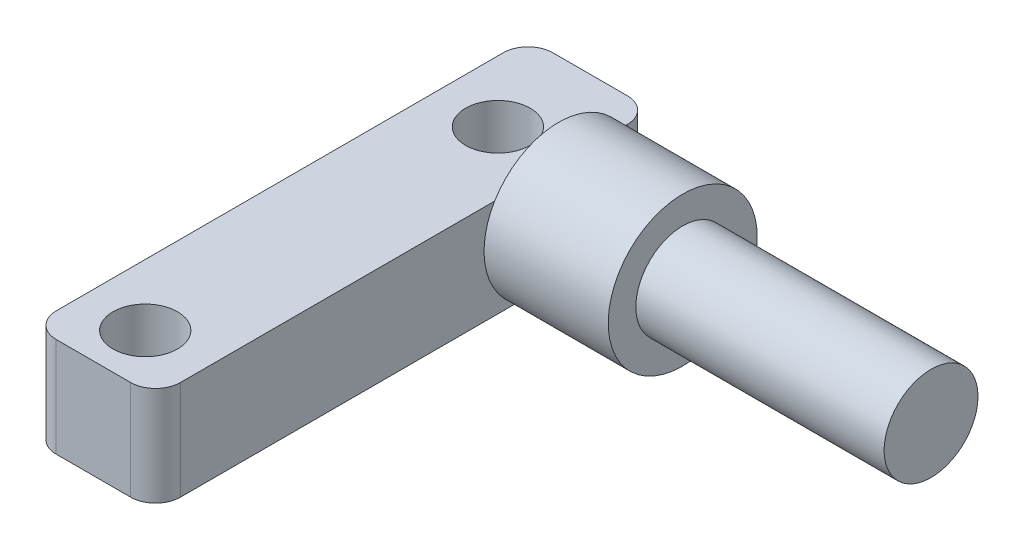
SolidWorks part; units mm, degrees
ref_plane "Front Plane" through (0, 0, 0) normal (0, 0, 1) x (1, 0, 0)
ref_plane "Top Plane" through (0, 0, 0) normal (0, 1, 0) x (1, 0, 0)
ref_plane "Right Plane" through (0, 0, 0) normal (1, 0, 0) x (0, 0, -1)
sketch "Sketch1" plane through (0, 0, 0) normal (0, 1, 0) x (1, 0, 0)
  line L0 (-3.5227, -7.2529) -> (-3.5227, -32.6529)
extrude "Extrude-Thin1" add sketch "Sketch1" along normal blind 5.08 thin contours L0 thin type one direction reverse wall 6.35
fillet "Fillet4" radius 1.27 1 edges at (-3.5227, 2.54, 32.6529)
fillet "Fillet5" radius 1.27 1 edges at (2.8273, 2.54, 32.6529)
fillet "Fillet6" radius 1.27 2 edges at (-3.5227, 2.54, 7.2529) (2.8273, 2.54, 7.2529)
sketch "Sketch5" plane through (0, 5.08, 0) normal (0, 1, 0) x (1, 0, 0)
  circle A0 centre (-0.381, -29.972) radius 1.651
extrude "Cut-Extrude1" cut sketch "Sketch5" against normal blind 6.35
sketch "Sketch8" plane through (2.8273, 0, 0) normal (1, 0, 0) x (0, 0, -1)
  circle A0 centre (-12.0425, 3.1242) radius 3.81
extrude "Boss-Extrude1" add sketch "Sketch8" along normal blind 6.35
sketch "Sketch12" plane through (2.8273, 0, 0) normal (1, 0, 0) x (0, 0, -1)
  circle A0 centre (-12.0425, 3.1242) radius 2.4
extrude "Boss-Extrude2" add sketch "Sketch12" along normal blind 19.05
pattern_linear "LPattern1" count 2 spacing 18.034 along (0, 0, -1) of "Cut-Extrude1"
